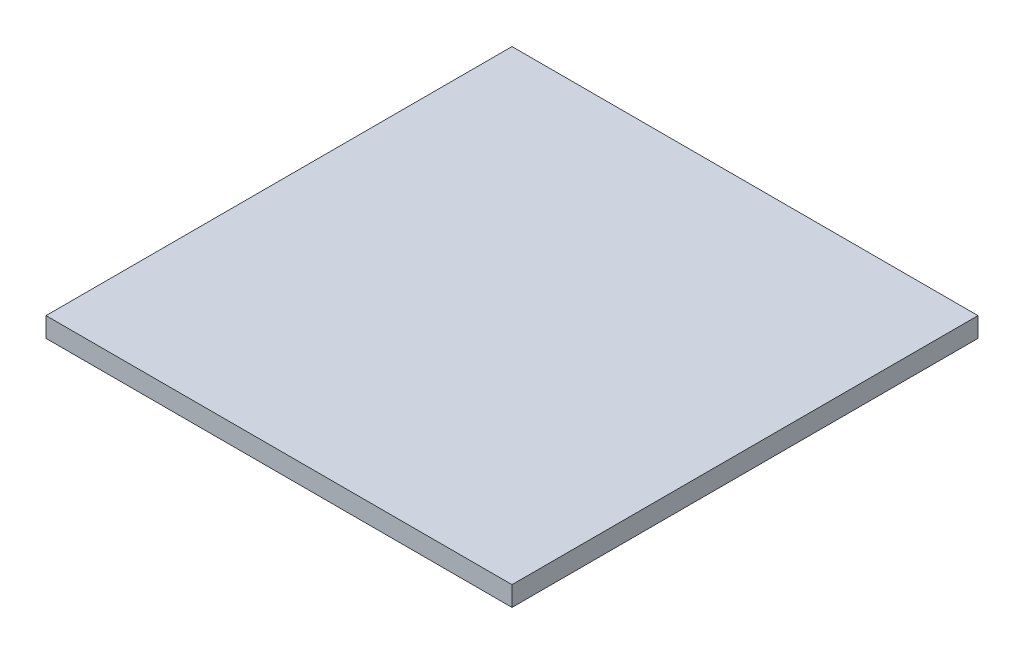
SolidWorks part; units mm, degrees
ref_plane "Front Plane" through (0, 0, 0) normal (0, 0, 1) x (1, 0, 0)
ref_plane "Top Plane" through (0, 0, 0) normal (0, 1, 0) x (1, 0, 0)
ref_plane "Right Plane" through (0, 0, 0) normal (1, 0, 0) x (0, 0, -1)
sketch "Sketch1" plane through (0, 0, 0) normal (0, 1, 0) x (1, 0, 0)
  line L1 (-149.85, 149.85) -> (149.85, 149.85)
  line L2 (-149.85, 149.85) -> (-149.85, -149.85)
  line L3 (-149.85, -149.85) -> (149.85, -149.85)
  line L4 (149.85, 149.85) -> (149.85, -149.85)
  line L5 (-149.85, 149.85) -> (149.85, -149.85) construction
  line L6 (-149.85, -149.85) -> (149.85, 149.85) construction
  point P0 (0, 0)
  dimension "D1" = 299.7
  dimension "D2" = 299.7
extrude "Boss-Extrude1" add sketch "Sketch1" along normal blind 12.7
